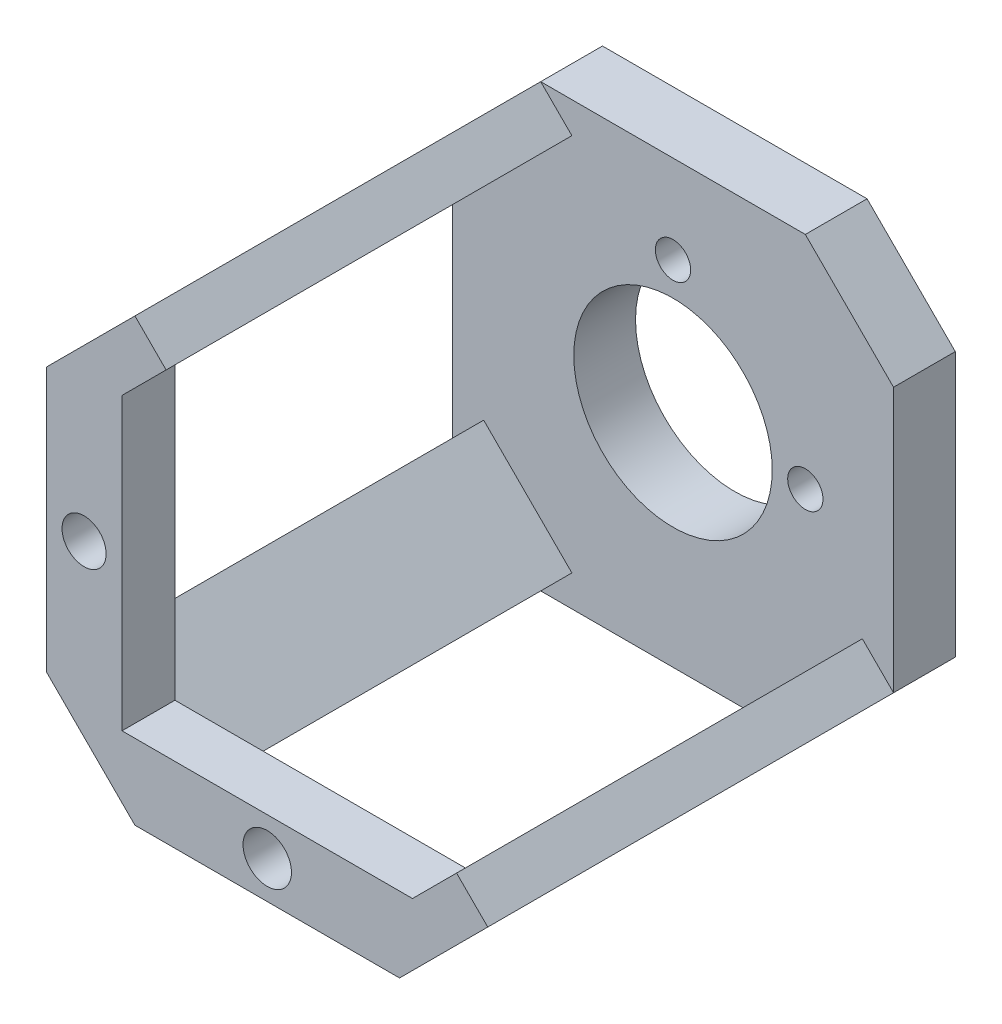
SolidWorks part; units mm, degrees
ref_plane "Plan de face" through (0, 0, 0) normal (0, 0, 1) x (1, 0, 0)
ref_plane "Plan de dessus" through (0, 0, 0) normal (0, 1, 0) x (1, 0, 0)
ref_plane "Plan de droite" through (0, 0, 0) normal (1, 0, 0) x (0, 0, -1)
sketch "Esquisse1" plane through (0, 0, 0) normal (0, 0, 1) x (1, 0, 0)
  line L1 (-26.8836, 22.9873) -> (23.1164, 22.9873)
  line L2 (-26.8836, 22.9873) -> (-26.8836, -27.0127)
  line L3 (-26.8836, -27.0127) -> (23.1164, -27.0127)
  line L4 (23.1164, 22.9873) -> (23.1164, -27.0127)
  dimension "D1" = 50
  dimension "D2" = 50
extrude "Boss.-Extru.1" add sketch "Esquisse1" along normal blind 7 contours L3 L4 L1 L2
chamfer "Chanfrein1" distance 10 angle 45 4 edges at (-26.8836, 22.9873, 3.5) (23.1164, 22.9873, 3.5) (-26.8836, -27.0127, 3.5) (23.1164, -27.0127, 3.5)
sketch "Esquisse2" plane through (0, 0, 7) normal (0, 0, 1) x (1, 0, 0)
  line L0 (-26.8836, -17.0127) -> (-16.8836, -27.0127)
  line L1 (-16.8836, -27.0127) -> (-13.348, -23.4772)
  line L2 (-13.348, -23.4772) -> (-23.348, -13.4772)
  line L3 (-23.348, -13.4772) -> (-26.8836, -17.0127)
  line L4 (-26.8836, 12.9873) -> (-16.8836, 22.9873)
  line L5 (-16.8836, 22.9873) -> (-13.348, 19.4518)
  line L6 (-13.348, 19.4518) -> (-23.348, 9.4518)
  line L7 (-23.348, 9.4518) -> (-26.8836, 12.9873)
  line L8 (23.1164, -17.0127) -> (19.5809, -13.4772)
  line L9 (19.5809, -13.4772) -> (9.5809, -23.4772)
  line L10 (9.5809, -23.4772) -> (13.1164, -27.0127)
  line L11 (-16.8836, -27.0127) -> (13.1164, -27.0127) construction
  line L12 (13.1164, -27.0127) -> (23.1164, -17.0127) construction
  line L13 (13.1164, -27.0127) -> (23.1164, -17.0127)
  line M8 (-16.8836, 22.9873) -> (-26.8836, 12.9873)
  line M12 (13.1164, -27.0127) -> (23.1164, -17.0127)
  dimension "D1" = 5
  dimension "D2" = 5
  dimension "D3" = 5
  dimension "D4" = 5
  dimension "D5" = 5
  dimension "D6" = 5
extrude "Boss.-Extru.2" add sketch "Esquisse2" along normal blind 40 contours L7 L6 L5 M8 | L9 L10 L8 M12 | L2 L3 L0 L1
ref_plane "Plan1" through (0, 0, 47) normal (0, 0, 1) x (1, 0, 0)
sketch "Esquisse4" plane through (0, 0, 47) normal (0, 0, 1) x (1, 0, 0)
  line L0 (-18.348, 14.4518) -> (-13.348, 19.4518)
  line L1 (-13.348, 19.4518) -> (-23.348, 9.4518) construction
  line L2 (-13.348, 19.4518) -> (-16.8836, 22.9873)
  line L3 (-16.8836, 22.9873) -> (-26.8836, 12.9873)
  line L4 (-26.8836, 12.9873) -> (-26.8836, -17.0127)
  line L5 (-26.8836, -17.0127) -> (-16.8836, -27.0127)
  line L6 (-16.8836, -27.0127) -> (13.1164, -27.0127)
  line L7 (13.1164, -27.0127) -> (23.1164, -17.0127)
  line L8 (23.1164, -17.0127) -> (19.5809, -13.4772)
  line L9 (19.5809, -13.4772) -> (14.5809, -18.4772)
  line L10 (19.5809, -13.4772) -> (9.5809, -23.4772) construction
  line L11 (14.5809, -18.4772) -> (-18.348, -18.4772)
  line L12 (-13.348, -23.4772) -> (-23.348, -13.4772) construction
  line L13 (-18.348, -18.4772) -> (-18.348, 14.4518)
extrude "Boss.-Extru.3" add sketch "Esquisse4" along normal blind 6
sketch "Esquisse5" plane through (0, 0, 0) normal (0, 0, -1) x (-1, 0, 0)
  line L0 (-23.1164, 12.9873) -> (-23.1164, -17.0127) construction
  line L1 (16.8836, 22.9873) -> (-13.1164, 22.9873) construction
  circle A0 centre (1.8836, -2.0127) radius 11.25
  point P2 (-23.1164, -2.0127)
  dimension "D3" = 22.5
  dimension "D1" = 25
  dimension "D2" = 25
extrude "Enlèv. mat.-Extru.1" cut sketch "Esquisse5" against normal up to surface (7 mm away) contours A0 up to face at (-4.2356, -4.3648, 7)
sketch "Esquisse6" plane through (0, 0, 53) normal (0, 0, 1) x (1, 0, 0)
  line L0 (-18.348, -18.4772) -> (-18.348, 14.4518) construction
  line L2 (14.5809, -18.4772) -> (-18.348, -18.4772) construction
  line L3 (-26.8836, 12.9873) -> (-26.8836, -17.0127) construction
  line L4 (23.1164, 12.9873) -> (23.1164, -17.0127) construction
  line L5 (-16.8836, -27.0127) -> (13.1164, -27.0127) construction
  circle A0 centre (-22.648, -2.0127) radius 2.5
  circle A1 centre (-1.8836, -22.7772) radius 2.745
  dimension "D3" = 5
  dimension "D1" = 4.3
  dimension "D2" = 4.3
  dimension "D4" = 25
  dimension "D5" = 25
  dimension "D6" = 25
  dimension "D7" = 4.2355
  dimension "D8" = 4.2355
extrude "Enlèv. mat.-Extru.2" cut sketch "Esquisse6" against normal up to surface (6 mm away) up to face at (-22.4432, -4.3401, 47)
sketch "Esquisse7" plane through (0, 0, 0) normal (0, 0, -1) x (-1, 0, 0)
  line L1 (16.8836, 22.9873) -> (-13.1164, 22.9873) construction
  line L2 (16.8836, -27.0127) -> (-13.1164, -27.0127) construction
  line L3 (26.8836, 12.9873) -> (26.8836, -17.0127) construction
  circle A0 centre (-13.1164, -2.0127) radius 2
  circle A2 centre (1.8836, -2.0127) radius 11.25 construction
  circle A3 centre (1.8836, 12.9873) radius 2
  dimension "D3" = 15
  dimension "D4" = 4
  dimension "D5" = 4
  dimension "D6" = 15
  dimension "D7" = 25
  dimension "D1" = 25
  dimension "D2" = 25
extrude "Enlèv. mat.-Extru.3" cut sketch "Esquisse7" against normal up to surface (7 mm away) contours A3 | A0 up to face at (9.3664, -2.0127, 7)
